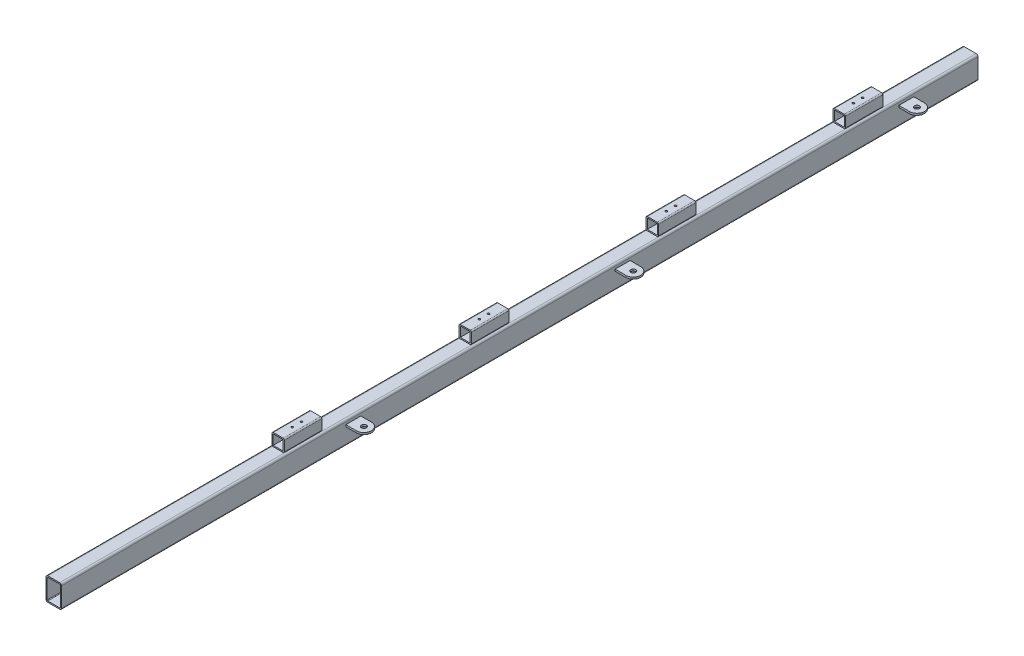
SolidWorks part; units mm, degrees
material "Alloy Steel"
ref_plane "Front" through (0, 0, 0) normal (0, 0, 1) x (1, 0, 0)
ref_plane "Top" through (0, 0, 0) normal (0, 1, 0) x (1, 0, 0)
ref_plane "Right" through (0, 0, 0) normal (1, 0, 0) x (0, 0, -1)
sketch "Sketch1" plane through (0, 0, 0) normal (0, 0, 1) x (1, 0, 0)
  line L0 (0, 40.8909) -> (0, -24.1212) construction
  line L1 (-9.5, 37) -> (9.5, 37)
  line L2 (-12.5, 34) -> (-12.5, 3)
  line L3 (-9.5, 0) -> (9.5, 0)
  line L4 (12.5, 34) -> (12.5, 3)
  arc A0 (-12.5, 3) -> (-9.5, 0) centre (-9.5, 3) ccw
  arc A1 (9.5, 0) -> (12.5, 3) centre (9.5, 3) ccw
  arc A2 (9.5, 37) -> (12.5, 34) centre (9.5, 34) cw
  arc A3 (-9.5, 37) -> (-12.5, 34) centre (-9.5, 34) ccw
  point P9 (-12.5, 0)
  point P12 (12.5, 0)
  point P15 (12.5, 37)
  dimension "D3" = 3
  dimension "D1" = 37
  dimension "D2" = 25
extrude "Extrude-Thin1" add sketch "Sketch1" along normal blind 1470 thin contours L1 A2 L4 A1 L3 A0 L2 A3
ref_plane "Plane1" through (0, 27, 0) normal (0, 1, 0) x (1, 0, 0)
sketch "Sketch2" plane through (0, 27, 0) normal (0, 1, 0) x (1, 0, 0)
  line L0 (29.5, -103) -> (12.5, -103)
  line L1 (12.5, -1470) -> (12.5, 0) construction
  line L2 (12.5, -103) -> (12.5, -127)
  line L3 (12.5, -127) -> (29.5, -127)
  line L4 (-9.5, 0) -> (9.5, 0) construction
  line L5 (29.5, -558) -> (12.5, -558)
  line L6 (12.5, -558) -> (12.5, -582)
  line L7 (12.5, -582) -> (29.5, -582)
  line L8 (29.5, -990) -> (12.5, -990)
  line L9 (12.5, -990) -> (12.5, -1014)
  line L10 (12.5, -1014) -> (29.5, -1014)
  arc A0 (29.5, -103) -> (29.5, -127) centre (29.5, -115) cw
  circle A1 centre (29.5, -115) radius 4
  arc A2 (29.5, -558) -> (29.5, -582) centre (29.5, -570) cw
  circle A3 centre (29.5, -570) radius 4
  arc A4 (29.5, -990) -> (29.5, -1014) centre (29.5, -1002) cw
  circle A5 centre (29.5, -1002) radius 4
  dimension "D1" = 8
  dimension "D2" = 12
  dimension "D5" = 8
  dimension "D6" = 12
  dimension "D9" = 8
  dimension "D10" = 12
  dimension "D3" = 17
  dimension "D4" = 115
  dimension "D8" = 570
  dimension "D12" = 1002
extrude "Boss-Extrude1" add sketch "Sketch2" along normal blind 3
ref_plane "Plane2" through (0, 0, 150) normal (0, 0, -1) x (-1, 0, 0)
sketch "Sketch3" plane through (0, 0, 150) normal (0, 0, -1) x (-1, 0, 0)
  line L0 (0, 62.5541) -> (0, 30.9171) construction
  line L1 (-8, 57) -> (8, 57)
  line L2 (-10, 55) -> (-10, 39)
  line L3 (-8, 37) -> (8, 37)
  line L4 (10, 55) -> (10, 39)
  line L5 (-10.5, 34) -> (-10.5, 3) construction
  line L6 (10.5, 34) -> (10.5, 3) construction
  line L7 (9.5, 37) -> (-9.5, 37) construction
  arc A0 (8, 37) -> (10, 39) centre (8, 39) ccw
  arc A1 (-10, 39) -> (-8, 37) centre (-8, 39) ccw
  arc A2 (-8, 57) -> (-10, 55) centre (-8, 55) ccw
  arc A3 (8, 57) -> (10, 55) centre (8, 55) cw
  point P14 (10, 37)
  point P21 (10, 57)
  dimension "D2" = 2
  dimension "D1" = 20
extrude "Extrude-Thin2" add sketch "Sketch3" against normal blind 60 thin contours L1 A3 L4 A0 L3 A1 L2 A2
ref_plane "Plane3" through (0, 0, 180) normal (0, 0, 1) x (1, 0, 0)
hole_wizard "M3 Clearance Hole1" positions "Sketch5" profile "Sketch6" hole size "M3" standard "DIN" end condition through all
sketch "Sketch5" plane through (0, 57, 0) normal (0, 1, 0) x (1, 0, 0)
  line L0 (-8, -180) -> (8, -180) construction
  line L1 (-8, -210) -> (-8, -150) construction
  line L2 (8, -210) -> (8, -150) construction
  line L4 (0, -210) -> (0, -150) construction
  line L5 (8, -210) -> (-8, -210) construction
  line L6 (8, -150) -> (-8, -150) construction
  point P0 (0, -187.45)
  point P2 (0, -172.55)
  dimension "D1" = 14.9
sketch "Sketch6" plane through (0, 57, 187.45) normal (1, 0, 0) x (0, 0, 1)
  line L0 (0, 0) -> (0, 57)
  line L1 (0, 57) -> (1.6, 57)
  line L2 (1.6, 57) -> (1.6, 0)
  line L5 (1.6, 0) -> (0, 0)
  line L11 (0, -6.35) -> (0, 107.95) construction
  dimension "Thru Hole Dia." = 3.2
  dimension "Thru Hole Depth" = 57
pattern_linear "LPattern1" count 4 spacing 300 along (0, 0, 1) of "Extrude-Thin2", "M3 Clearance Hole1"
